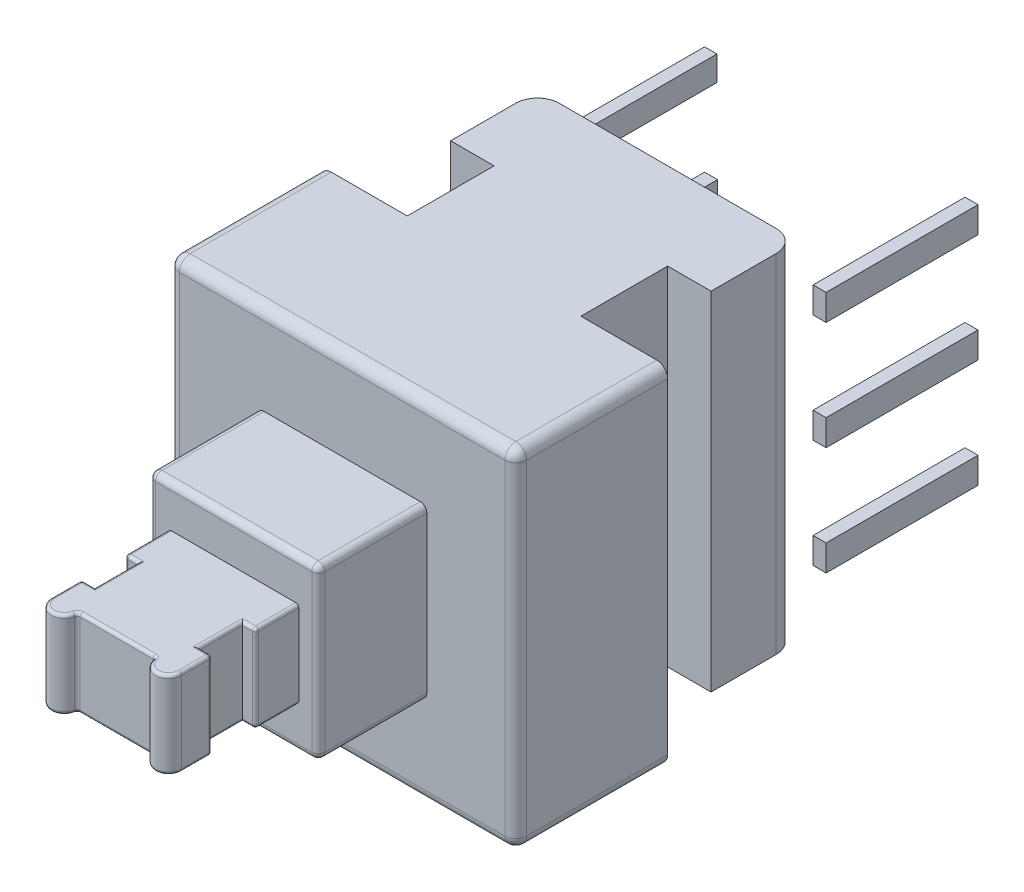
SolidWorks part; units mm, degrees
ref_plane "前基準面" through (0, 0, 0) normal (0, 0, 1) x (1, 0, 0)
ref_plane "上基準面" through (0, 0, 0) normal (0, 1, 0) x (1, 0, 0)
ref_plane "右基準面" through (0, 0, 0) normal (1, 0, 0) x (0, 0, -1)
sketch "草圖1" plane through (0, 0, 0) normal (0, 0, 1) x (1, 0, 0)
  line L1 (-4, -4) -> (4, -4)
  line L2 (-4, -4) -> (-4, 4)
  line L3 (-4, 4) -> (4, 4)
  line L4 (4, -4) -> (4, 4)
  line L5 (-4, -4) -> (4, 4) construction
  line L6 (-4, 4) -> (4, -4) construction
  point P0 (0, 0)
extrude "填料-伸長1" add sketch "草圖1" along normal blind 8
sketch "草圖3" plane through (0, 0, 8) normal (0, 0, 1) x (1, 0, 0)
  line L1 (-1.95, -1.95) -> (1.95, -1.95)
  line L2 (-1.95, -1.95) -> (-1.95, 1.95)
  line L3 (-1.95, 1.95) -> (1.95, 1.95)
  line L4 (1.95, -1.95) -> (1.95, 1.95)
  line L5 (-1.95, -1.95) -> (1.95, 1.95) construction
  line L6 (-1.95, 1.95) -> (1.95, -1.95) construction
  point P0 (0, 0)
extrude "填料-伸長2" add sketch "草圖3" along normal blind 2.5
sketch "草圖4" plane through (0, 0, 10.5) normal (0, 0, 1) x (1, 0, 0)
  line L1 (-1.5, 1) -> (1.5, 1)
  line L2 (-1.5, 1) -> (-1.5, -1)
  line L3 (-1.5, -1) -> (1.5, -1)
  line L4 (1.5, 1) -> (1.5, -1)
  line L5 (-1.5, 1) -> (1.5, -1) construction
  line L6 (-1.5, -1) -> (1.5, 1) construction
  point P0 (0, 0)
extrude "填料-伸長3" add sketch "草圖4" along normal blind 3
sketch "草圖5" plane through (0, 0, 0) normal (0, 0, -1) x (-1, 0, 0)
  line L0 (-3.15, -0.3) -> (-2.85, -0.3)
  line L1 (-3, -2.5) -> (3, -2.5) construction
  line L2 (-3, -2.5) -> (-3, 2.5) construction
  line L3 (-3, 2.5) -> (3, 2.5) construction
  line L4 (3, -2.5) -> (3, 2.5) construction
  line L5 (-3, -2.5) -> (3, 2.5) construction
  line L6 (-3, 2.5) -> (3, -2.5) construction
  line L7 (-3.15, 2.2) -> (-2.85, 2.2)
  line L8 (-3.15, 2.2) -> (-3.15, 2.8)
  line L9 (-3.15, 2.8) -> (-2.85, 2.8)
  line L10 (-2.85, 2.2) -> (-2.85, 2.8)
  line L11 (-3.15, 2.2) -> (-2.85, 2.8) construction
  line L12 (-3.15, 2.8) -> (-2.85, 2.2) construction
  line L13 (-3.15, -0.3) -> (-3.15, 0.3)
  line L14 (-3.15, 0.3) -> (-2.85, 0.3)
  line L15 (-2.85, -0.3) -> (-2.85, 0.3)
  line L16 (-3.15, -0.3) -> (-2.85, 0.3) construction
  line L17 (-3.15, 0.3) -> (-2.85, -0.3) construction
  line L18 (-3.15, -2.8) -> (-2.85, -2.8)
  line L19 (-3.15, -2.8) -> (-3.15, -2.2)
  line L20 (-3.15, -2.2) -> (-2.85, -2.2)
  line L21 (-2.85, -2.8) -> (-2.85, -2.2)
  line L22 (-3.15, -2.8) -> (-2.85, -2.2) construction
  line L23 (-3.15, -2.2) -> (-2.85, -2.8) construction
  line L24 (2.85, -2.8) -> (3.15, -2.8)
  line L25 (2.85, -2.8) -> (2.85, -2.2)
  line L26 (2.85, -2.2) -> (3.15, -2.2)
  line L27 (3.15, -2.8) -> (3.15, -2.2)
  line L28 (2.85, -2.8) -> (3.15, -2.2) construction
  line L29 (2.85, -2.2) -> (3.15, -2.8) construction
  line L30 (2.85, -0.3) -> (3.15, -0.3)
  line L31 (2.85, -0.3) -> (2.85, 0.3)
  line L32 (2.85, 0.3) -> (3.15, 0.3)
  line L33 (3.15, -0.3) -> (3.15, 0.3)
  line L34 (2.85, -0.3) -> (3.15, 0.3) construction
  line L35 (2.85, 0.3) -> (3.15, -0.3) construction
  line L36 (2.8647, 2.2295) -> (3.15, 2.2295)
  line L37 (2.8647, 2.2295) -> (2.8647, 2.8)
  line L38 (2.8647, 2.8) -> (3.15, 2.8)
  line L39 (3.15, 2.2295) -> (3.15, 2.8)
  line L40 (2.8647, 2.2295) -> (3.15, 2.8) construction
  line L41 (2.8647, 2.8) -> (3.15, 2.2295) construction
  point P0 (0, 0)
extrude "填料-伸長4" add sketch "草圖5" along normal blind 3.5
sketch "草圖6" plane through (0, -1, 0) normal (0, -1, 0) x (1, 0, 0)
  line L0 (0, 13.5) -> (0, 12.5) construction
  line L1 (-1.5, 13.5) -> (1.5, 13.5) construction
  line L2 (0, 12.5) -> (1.2, 12.5) construction
  line L3 (0, 12.5) -> (-1.2, 12.5) construction
  line L4 (-1.2, 12.5) -> (-1.2, 11.5)
  line L5 (1.2, 12.5) -> (1.2, 11.5)
  line L6 (1.2, 11.5) -> (1.5, 11.5)
  line L7 (1.5, 13.5) -> (1.5, 10.5) construction
  line L8 (1.5, 11.5) -> (1.5, 12.5)
  line L9 (1.5, 12.5) -> (1.2, 12.5)
  line L10 (-1.2, 12.5) -> (-1.5, 12.5)
  line L11 (-1.5, 13.5) -> (-1.5, 10.5) construction
  line L12 (-1.5, 12.5) -> (-1.5, 11.5)
  line L13 (-1.5, 11.5) -> (-1.2, 11.5)
extrude "除料-伸長1" cut sketch "草圖6" against normal up to surface (2 mm away) up to face at (0, 1, 12)
sketch "草圖7" plane through (0, -1, 0) normal (0, -1, 0) x (1, 0, 0)
  line L0 (0, 13.5) -> (0, 13.2) construction
  line L1 (-1.5, 13.5) -> (1.5, 13.5) construction
  line L2 (-1.5, 13.5) -> (-1.5, 12.5) construction
  line L4 (0, 13.2) -> (-1.5, 13.2) construction
  line L5 (0, 13.2) -> (-0.9, 13.2)
  line L6 (-1.5, 13.2) -> (-1.5, 13.5)
  line L7 (-1.5, 13.5) -> (0, 13.5)
  line L8 (0, 13.2) -> (1.5, 13.2) construction
  line L10 (1.5, 13.5) -> (1.5, 12.5) construction
  line L11 (0, 13.2) -> (0.9, 13.2)
  line L12 (0.9, 13.2) -> (0.8987, 13.1966)
  line L13 (1.5, 13.2) -> (1.5, 13.5)
  line L14 (1.5, 13.5) -> (0, 13.5)
  arc A0 (-1.5, 13.2) -> (-0.9, 13.2) centre (-1.2, 13.2) cw
  arc A1 (1.5, 13.2) -> (0.9, 13.2) centre (1.2, 13.2) ccw
  line M3 (-1.5, 13.5) -> (-1.5, 12.5)
  line M13 (1.5, 12.5) -> (1.5, 13.5)
  line M14 (1.5, 13.5) -> (-1.5, 13.5)
extrude "除料-伸長3" cut sketch "草圖7" against normal up to surface (2 mm away) contours A0 L7 M3 | A1 L14 A0 L5 L11 M14 | A1 M13 M14 up to face at (0, 1, 12)
fillet "圓角1" radius 0.25 12 edges at (0, -4, 0) (4, 0, 0) (-4, 0, 0) (0, 4, 0) (0, 4, 8) (-4, 4, 4) (-4, 0, 8) (-4, -4, 4) (4, -4, 4) (4, 4, 4) (4, 0, 8) (0, -4, 8)
fillet "圓角2" radius 0.15 8 edges at (1.95, 1.95, 9.25) (0, 1.95, 10.5) (-1.95, 1.95, 9.25) (-1.95, -1.95, 9.25) (1.95, -1.95, 9.25) (1.95, 0, 10.5) (0, -1.95, 10.5) (-1.95, 0, 10.5)
fillet "圓角3" radius 0.07 32 edges at (-1.2, 1, 13.5) (-1.2, -1, 13.5) (1.5, 1, 12.85) (1.5, -1, 12.85) (-1.5, 0, 12.5) (-1.5, 1, 12.85) (-1.5, -1, 12.85) (0.9, 0, 13.2) (-0.9, 0, 13.2) (1.2, 1, 13.5) (1.35, 1, 12.5) (1.2, 1, 12) (1.5, 0, 12.5) (1.35, -1, 12.5) (1.2, -1, 12) (-1.2, -1, 12) (-1.35, -1, 12.5) (1.2, -1, 13.5) (-1.35, 1, 12.5) (-1.2, 1, 12) (0, -1, 13.2) (0, 1, 13.2) (-1.5, 1, 11) (-1.35, 1, 11.5) (1.35, 1, 11.5) (1.5, -1, 11) (1.5, 1, 11) (1.5, 0, 11.5) (1.35, -1, 11.5) (-1.35, -1, 11.5) (-1.5, 0, 11.5) (-1.5, -1, 11)
sketch "草圖9" plane through (0, -4, 0) normal (0, -1, 0) x (1, 0, 0)
  line L0 (-4, 0) -> (-4, 4.5)
  line L1 (-4, 0.25) -> (-4, 7.75) construction
  line L2 (-4, 0) -> (4, 0)
  line L3 (-4, 4.5) -> (-2, 4.5)
  line L4 (-2, 4.5) -> (-2, 2.5)
  line L5 (-2, 2.5) -> (-3, 2.5)
  line L6 (-3, 2.5) -> (-3, 1)
  line L7 (4, 0) -> (4, 4.5)
  line L8 (4, 7.75) -> (4, 0.25) construction
  line L9 (4, 4.5) -> (2, 4.5)
  line L10 (2, 4.5) -> (2, 2.5)
  line L11 (2, 2.5) -> (3, 2.5)
  line L12 (3, 2.5) -> (3, 1)
  line L13 (2.5, 0.5) -> (-2.5, 0.5)
  arc A0 (2.5, 0.5) -> (3, 1) centre (2.5, 1) ccw
  arc A1 (-3, 1) -> (-2.5, 0.5) centre (-2.5, 1) ccw
  dimension "D1" = 0.5
extrude "除料-伸長5" cut sketch "草圖9" against normal through all
